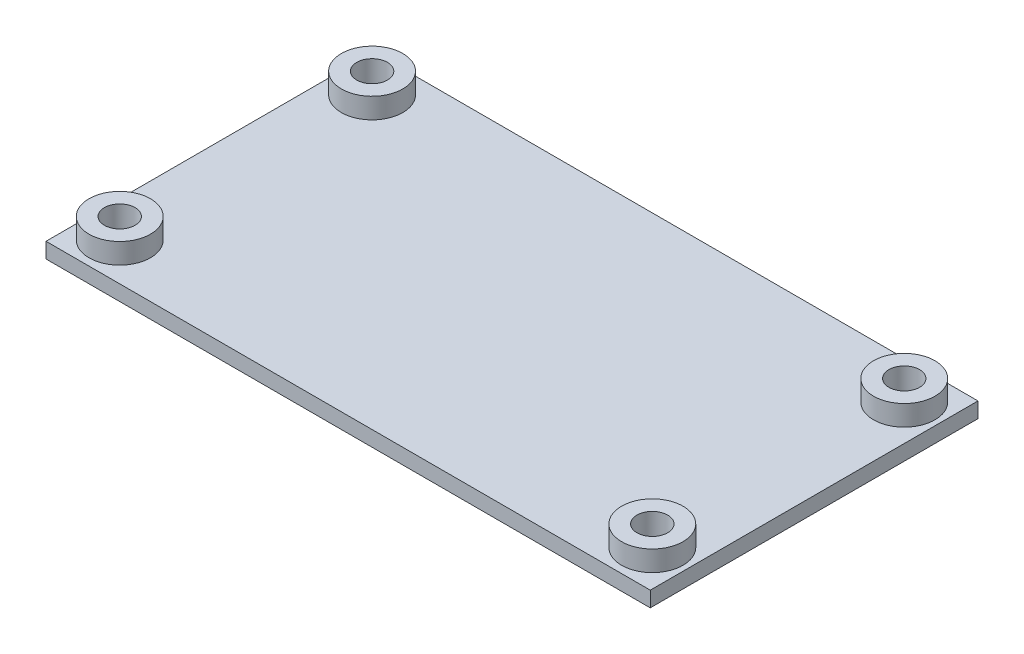
SolidWorks part; units mm, degrees
material "ABS PC"
ref_plane "前视基准面" through (0, 0, 0) normal (0, 0, 1) x (1, 0, 0)
ref_plane "上视基准面" through (0, 0, 0) normal (0, 1, 0) x (1, 0, 0)
ref_plane "右视基准面" through (0, 0, 0) normal (1, 0, 0) x (0, 0, -1)
sketch "草图2" plane through (0, 0, 0) normal (0, 1, 0) x (1, 0, 0)
  line L1 (-24.6381, 15.6657) -> (32.3619, 15.6657)
  line L2 (-24.6381, 15.6657) -> (-24.6381, -24.7343)
  line L3 (-24.6381, -24.7343) -> (32.3619, -24.7343)
  line L4 (32.3619, 15.6657) -> (32.3619, -24.7343)
  dimension "D1" = 57
  dimension "D2" = 40.4
extrude "凸台-拉伸1" add sketch "草图2" along normal blind 1.5
sketch "草图4" plane through (0, 1.5, 0) normal (0, 1, 0) x (1, 0, 0)
  line L0 (-24.6381, 15.6657) -> (-24.6381, -24.7343) construction
  circle A0 centre (-22.0994, 7.7657) radius 1.5
  circle A1 centre (-22.1381, 7.7657) radius 1.5 construction
  circle A2 centre (-22.0994, 7.7657) radius 3
  circle A3 centre (-22.1381, -16.8343) radius 1.5
  circle A4 centre (-22.1381, -16.8343) radius 1.5 construction
  circle A5 centre (-22.1381, -16.8343) radius 3
  circle A9 centre (29.8619, -16.8343) radius 1.5
  circle A10 centre (29.8619, -16.8343) radius 1.5 construction
  circle A11 centre (29.8619, -16.8343) radius 3
  circle A14 centre (29.8619, 7.7657) radius 1.5
  circle A15 centre (29.8619, 7.7657) radius 1.5 construction
  circle A16 centre (29.8619, 7.7657) radius 3
  dimension "D1" = 0
  dimension "D2" = 3
  dimension "D5" = 2.5387
  dimension "D6" = 6
  dimension "D7" = 0
  dimension "D8" = 3
  dimension "D9" = 6
  dimension "D10" = 0
  dimension "D11" = 3
  dimension "D12" = 6
  dimension "D13" = 0
  dimension "D14" = 6
  dimension "D15" = 3
  dimension "D3" = 0
  dimension "D4" = 2.5387
extrude "凸台-拉伸3" add sketch "草图4" along normal blind 4
sketch "草图5" plane through (0, 1.5, 0) normal (0, 1, 0) x (1, 0, 0)
  line L0 (32.3619, 15.6657) -> (-24.6381, 15.6657) construction
  line L1 (-24.6381, 15.6657) -> (32.3619, 15.6657)
  line L2 (-24.6381, 15.6657) -> (-24.6381, 11.4657)
  line L3 (-24.6381, 11.4657) -> (32.3619, 11.4657)
  line L4 (32.3619, 15.6657) -> (32.3619, 11.4657)
  line L5 (-24.6381, 15.6657) -> (-24.6381, 9.3641) construction
  line L6 (32.3619, 9.424) -> (32.3619, 15.6657) construction
  line L7 (32.3619, 10.6657) -> (-24.6381, 10.6657) construction
  line L8 (-24.6381, -18.4926) -> (-24.6381, -24.7343) construction
  line L9 (-24.6381, -20.5343) -> (32.3619, -20.5343)
  line L10 (-24.6381, -20.5343) -> (-24.6381, -24.7343)
  line L11 (-24.6381, -24.7343) -> (32.3619, -24.7343)
  line L12 (32.3619, -20.5343) -> (32.3619, -24.7343)
  line L13 (32.3619, -24.7343) -> (32.3619, -18.4926) construction
  line L14 (-24.6381, -24.7343) -> (32.3619, -24.7343) construction
  line L15 (-24.6381, -19.7343) -> (32.3619, -19.7343) construction
  dimension "D1" = 0
  dimension "D2" = 0
  dimension "D3" = 0
  dimension "D4" = 0.8
  dimension "D5" = 0
  dimension "D6" = 0
  dimension "D7" = 0
  dimension "D8" = 0.8
extrude "切除-拉伸1" cut sketch "草图5" against normal through all
sketch "草图6" plane through (0, 1.5, 0) normal (0, 1, 0) x (1, 0, 0)
  line L0 (-24.6381, 11.4657) -> (-24.6381, 9.3641) construction
  line L1 (-25.6381, 11.4657) -> (-24.6381, 11.4657)
  line L2 (-25.6381, 11.4657) -> (-25.6381, -20.5343)
  line L3 (-25.6381, -20.5343) -> (-24.6381, -20.5343)
  line L4 (-24.6381, 11.4657) -> (-24.6381, -20.5343)
  line L5 (-24.6381, 11.4657) -> (32.3619, 11.4657) construction
  line L6 (32.3619, -20.5343) -> (-24.6381, -20.5343) construction
  line L7 (32.3619, -15.176) -> (32.3619, 6.1074) construction
  line L8 (32.3619, 11.4657) -> (33.3619, 11.4657)
  line L9 (32.3619, 11.4657) -> (32.3619, -20.5343)
  line L10 (32.3619, -20.5343) -> (33.3619, -20.5343)
  line L11 (33.3619, 11.4657) -> (33.3619, -20.5343)
  dimension "D1" = 0
  dimension "D2" = 0
  dimension "D3" = 0
  dimension "D4" = 1
  dimension "D5" = 0
  dimension "D6" = 0
  dimension "D7" = 0
  dimension "D8" = 1
extrude "凸台-拉伸4" add sketch "草图6" against normal up to surface (1.5 mm away) up to face at (3.8619, 0, 4.5343)
sketch "草图7" plane through (0, 0, 0) normal (0, -1, 0) x (1, 0, 0)
  circle A0 centre (29.8619, 16.8343) radius 1.5 construction
  circle A1 centre (29.8619, -7.7657) radius 1.5 construction
  circle A2 centre (-22.0994, -7.7657) radius 1.5 construction
  circle A3 centre (-22.1381, 16.8343) radius 1.5 construction
  circle A4 centre (29.8619, 16.8343) radius 1.5
  circle A5 centre (29.8619, -7.7657) radius 1.5
  circle A6 centre (-22.0994, -7.7657) radius 1.5
  circle A7 centre (-22.1381, 16.8343) radius 1.5
sketch "草图8" plane through (0, 5.5, 0) normal (0, 1, 0) x (1, 0, 0)
  circle A0 centre (-22.1381, -16.8343) radius 3 construction
  circle A1 centre (29.8619, -16.8343) radius 3 construction
  circle A2 centre (29.8619, -16.8343) radius 1.5 construction
  circle A3 centre (29.8619, 7.7657) radius 1.5 construction
  circle A4 centre (29.8619, 7.7657) radius 3 construction
  circle A5 centre (-22.0994, 7.7657) radius 1.5 construction
  circle A6 centre (-22.0994, 7.7657) radius 3 construction
  circle A7 centre (-22.1381, -16.8343) radius 3
  circle A8 centre (29.8619, -16.8343) radius 3
  circle A9 centre (29.8619, -16.8343) radius 1.5
  circle A10 centre (29.8619, 7.7657) radius 1.5
  circle A11 centre (29.8619, 7.7657) radius 3
  circle A12 centre (-22.0994, 7.7657) radius 1.5
  circle A13 centre (-22.0994, 7.7657) radius 3
extrude "切除-拉伸3" cut sketch "草图8" against normal blind 2
extrude "切除-拉伸4" cut sketch "草图7" against normal through all
